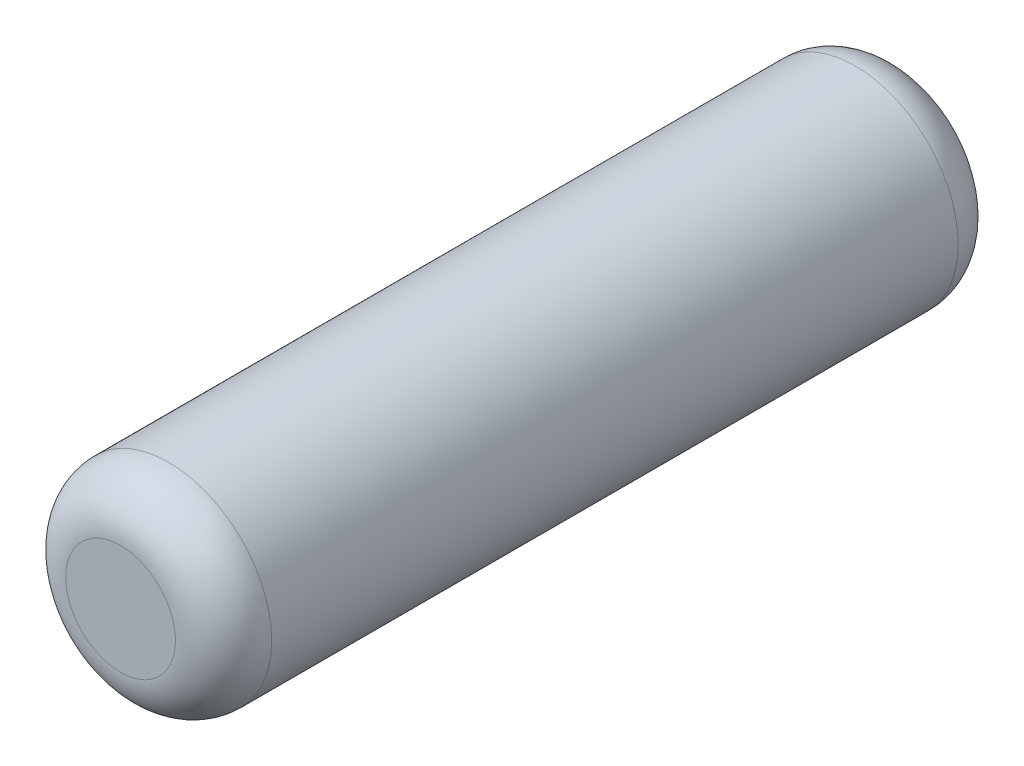
SolidWorks part; units mm, degrees
ref_plane "Front" through (0, 0, 0) normal (0, 0, 1) x (1, 0, 0)
ref_plane "Top" through (0, 0, 0) normal (0, 1, 0) x (1, 0, 0)
ref_plane "Right" through (0, 0, 0) normal (1, 0, 0) x (0, 0, -1)
sketch "Sketch1" plane through (0, 0, 0) normal (0, 0, 1) x (1, 0, 0)
  circle A0 centre (0, 0) radius 0.75
  dimension "D1" = 1.5
extrude "Boss-Extrude1" add sketch "Sketch1" along normal mid plane 5.7
fillet "Fillet1" radius 0.35 2 edges at (0.75, 0, -2.85) (0.75, 0, 2.85)
